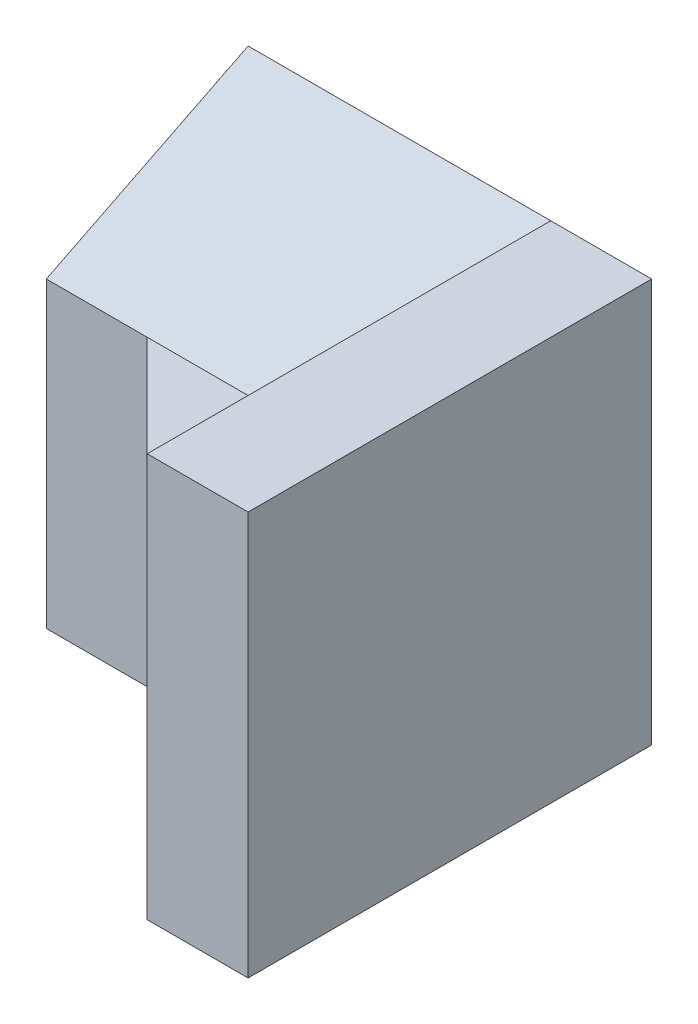
SolidWorks part; units mm, degrees
ref_plane "Front Plane" through (0, 0, 0) normal (0, 0, 1) x (1, 0, 0)
ref_plane "Top Plane" through (0, 0, 0) normal (0, 1, 0) x (1, 0, 0)
ref_plane "Right Plane" through (0, 0, 0) normal (1, 0, 0) x (0, 0, -1)
sketch "Sketch1" plane through (0, 0, 0) normal (1, 0, 0) x (0, 0, -1)
  line L1 (0, 0) -> (2, 0)
  line L2 (0, 0) -> (0, 3)
  line L3 (0, 3) -> (2, 4)
  line L4 (2, 0) -> (2, 4)
  dimension "D1" = 2
  dimension "D2" = 4
  dimension "D3" = 3
extrude "Boss-Extrude1" add sketch "Sketch1" along normal blind 3
sketch "Sketch2" plane through (3, 0, 0) normal (1, 0, 0) x (0, 0, -1)
  line L1 (-2, 0) -> (2, 0)
  line L2 (-2, 0) -> (-2, 4)
  line L3 (-2, 4) -> (2, 4)
  line L4 (2, 0) -> (2, 4)
  dimension "D1" = 4
extrude "Boss-Extrude2" add sketch "Sketch2" along normal blind 1
sketch "Sketch3" plane through (3, 0, 0) normal (-1, 0, 0) x (0, 0, 1)
  line L1 (0, 3) -> (2, 3)
  line L2 (0, 3) -> (0, 1.2587)
  line L3 (0, 1.2587) -> (2, 1.2587)
  line L4 (2, 3) -> (2, 1.2587)
  dimension "D1" = 2
extrude "Boss-Extrude3" add sketch "Sketch3" along normal blind 2
sketch "Sketch4" plane through (0, 3, 0) normal (0, 1, 0) x (1, 0, 0)
  line L0 (1, 0) -> (3, -2)
  line L1 (3, -2) -> (1, -2)
  line L2 (1, -2) -> (1, 0)
extrude "Cut-Extrude1" cut sketch "Sketch4" against normal blind 2
